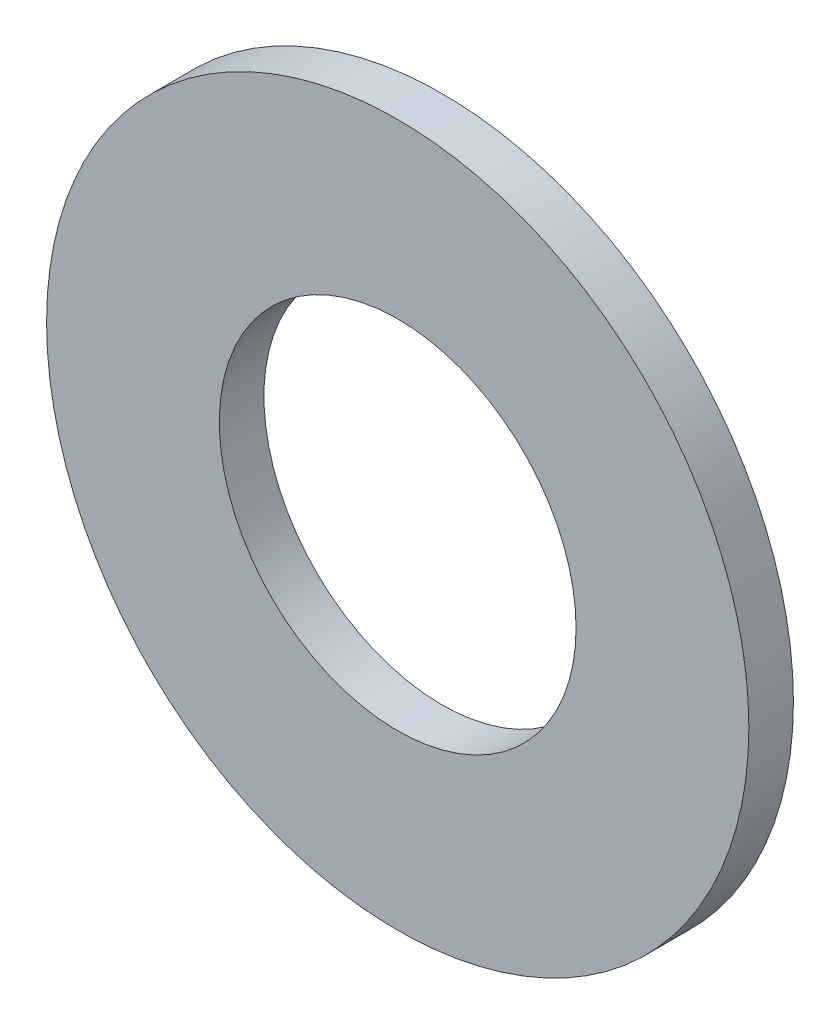
SolidWorks part; units mm, degrees
ref_plane "Front Plane" through (0, 0, 0) normal (1, 0, 0) x (0, 1, 0)
ref_plane "Top Plane" through (0, 0, 0) normal (0, 0, 1) x (0, 1, 0)
ref_plane "Right Plane" through (0, 0, 0) normal (0, 1, 0) x (-1, 0, 0)
sketch "Sketch1" plane through (0, 0, 0) normal (0, 0, 1) x (0, 1, 0)
  circle A0 centre (0, 0) radius 1.6
  circle A1 centre (0, 0) radius 3.15
  dimension "D1" = 6.3
  dimension "D2" = 3.2
extrude "Boss-Extrude1" add sketch "Sketch1" along normal blind 0.4
